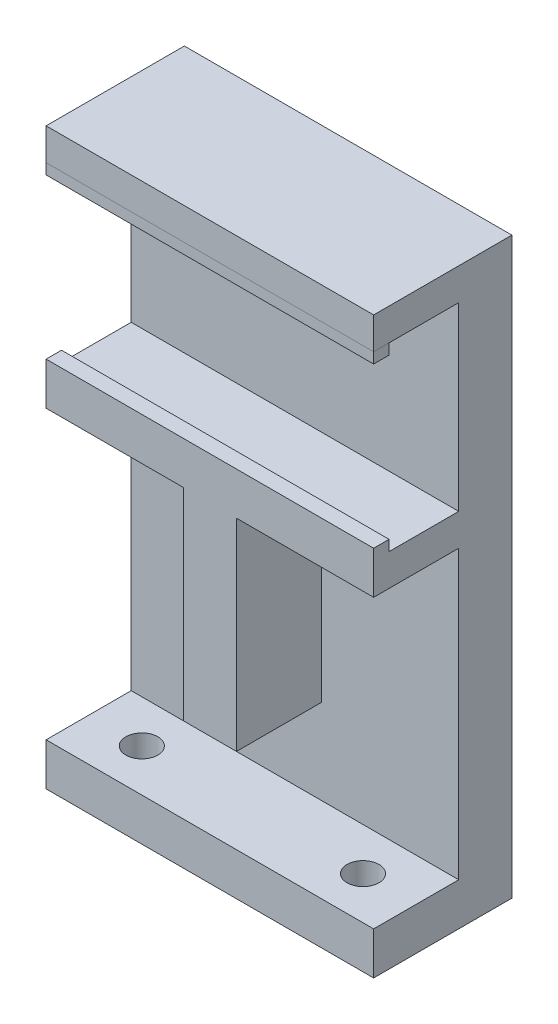
SolidWorks part; units mm, degrees
material "1060 合金"
ref_plane "前视基准面" through (0, 0, 0) normal (0, 0, 1) x (1, 0, 0)
ref_plane "上视基准面" through (0, 0, 0) normal (0, 1, 0) x (1, 0, 0)
ref_plane "右视基准面" through (0, 0, 0) normal (1, 0, 0) x (0, 0, -1)
sketch "草图1" plane through (0, 0, 0) normal (0, 0, 1) x (1, 0, 0)
  line L1 (0, 0) -> (30.8, 0)
  line L2 (0, 0) -> (0, 39)
  line L3 (0, 39) -> (30.8, 39)
  line L4 (30.8, 0) -> (30.8, 39)
  dimension "D1" = 30.8
  dimension "D2" = 39
extrude "凸台-拉伸1" add sketch "草图1" along normal blind 5
sketch "草图2" plane through (0, 0, 5) normal (0, 0, 1) x (1, 0, 0)
  line L0 (-5.69, 30.5) -> (26.1415, 30.5) construction
  line L1 (0, 0) -> (30.8, 0) construction
  line L2 (30.8, 0) -> (30.8, 39) construction
  line L3 (0, 39) -> (0, 42)
  line L4 (0, 42) -> (30.8, 42)
  line L5 (0, 39) -> (30.8, 39)
  line L6 (30.8, 42) -> (30.8, 39)
  line L7 (0, 39) -> (0, 0) construction
  line L8 (0, 22) -> (30.8, 22)
  line L9 (0, 22) -> (0, 19)
  line L10 (0, 19) -> (30.8, 19)
  line L11 (30.8, 22) -> (30.8, 19)
  dimension "D1" = 30.5
  dimension "D2" = 8.5
  dimension "D3" = 8.5
  dimension "D4" = 3
  dimension "D5" = 3
extrude "凸台-拉伸2" add sketch "草图2" along normal blind 8
sketch "草图3" plane through (0, 0, 5) normal (0, 0, 1) x (1, 0, 0)
  line L0 (0, 0) -> (30.8, 0) construction
  line L1 (12.9, 0) -> (17.9, 0)
  line L2 (12.9, 0) -> (12.9, 19)
  line L3 (12.9, 19) -> (17.9, 19)
  line L4 (17.9, 0) -> (17.9, 19)
  line L5 (0, 19) -> (30.8, 19) construction
  point P8 (15.4, 0)
  dimension "D1" = 5
  dimension "D2" = 2.5
extrude "凸台-拉伸3" add sketch "草图3" along normal blind 8
sketch "草图4" plane through (30.8, 0, 0) normal (1, 0, 0) x (0, 0, -1)
  line L0 (-5, 0) -> (-5, -8)
  line L1 (-5, -8) -> (-13, -8)
  line L2 (-13, -8) -> (-13, -12)
  line L3 (-13, -12) -> (0, -12)
  line L4 (0, -12) -> (0, 0)
  line L5 (-5, 0) -> (0, 0)
  dimension "D1" = 8
  dimension "D2" = 4
extrude "凸台-拉伸4" add sketch "草图4" against normal up to surface (30.8 mm away) up to face at (0, 22.25, 6.75)
sketch "草图5" plane through (0, -8, 0) normal (0, 1, 0) x (1, 0, 0)
  line L0 (0, -13) -> (0, -5) construction
  line L1 (30.8, -5) -> (30.8, -13) construction
  line L2 (0, -5) -> (30.8, -5) construction
  circle A0 centre (5, -9) radius 1.5
  circle A1 centre (25.8, -9) radius 1.5
  dimension "D1" = 3
  dimension "D2" = 5
  dimension "D3" = 5
  dimension "D4" = 4
  dimension "D5" = 4
extrude "切除-拉伸1" cut sketch "草图5" against normal up to next (4 mm away)
sketch "草图6" plane through (30.8, 0, 0) normal (1, 0, 0) x (0, 0, -1)
  line L1 (-13, 39) -> (-11.55, 39)
  line L2 (-13, 39) -> (-13, 38)
  line L3 (-13, 38) -> (-11.55, 38)
  line L4 (-11.55, 39) -> (-11.55, 38)
  line L5 (-13, 22) -> (-11.55, 22)
  line L6 (-13, 22) -> (-13, 23)
  line L7 (-13, 23) -> (-11.55, 23)
  line L8 (-11.55, 22) -> (-11.55, 23)
  dimension "D1" = 1
  dimension "D2" = 1.45
  dimension "D3" = 1
  dimension "D4" = 1.45
extrude "凸台-拉伸5" add sketch "草图6" against normal through all
sketch "草图7" plane through (0, 0, 5) normal (0, 0, -1) x (-1, 0, 0)
  line L1 (-30.8, 42) -> (0, 42)
  line L2 (-30.8, 42) -> (-30.8, 39)
  line L3 (-30.8, 39) -> (0, 39)
  line L4 (0, 42) -> (0, 39)
  dimension "D1" = 30.8
extrude "凸台-拉伸6" add sketch "草图7" along normal blind 5
